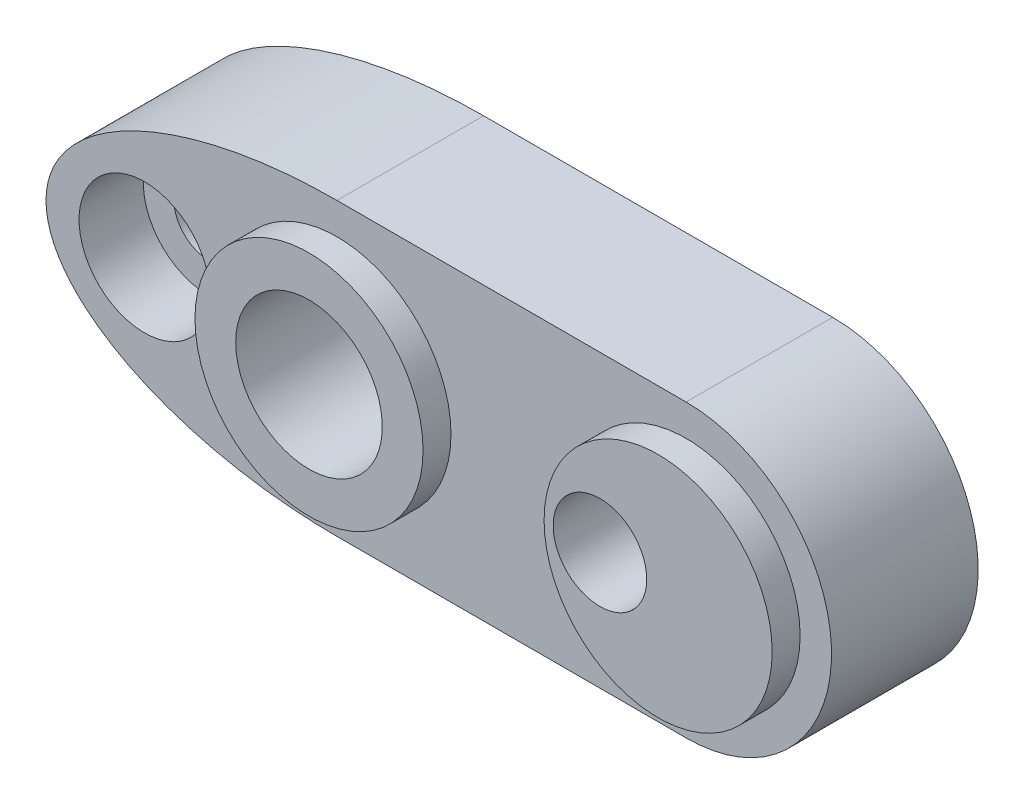
SolidWorks part; units mm, degrees
ref_plane "Front" through (0, 0, 0) normal (0, 0, 1) x (1, 0, 0)
ref_plane "Top" through (0, 0, 0) normal (0, 1, 0) x (1, 0, 0)
ref_plane "Right" through (0, 0, 0) normal (1, 0, 0) x (0, 0, -1)
sketch "Sketch1" plane through (0, 0, 0) normal (0, 0, 1) x (1, 0, 0)
  line L0 (0, 7.9375) -> (19.05, 7.9375)
  line L3 (0, -7.9375) -> (19.05, -7.9375)
  arc A2 (0, 7.9375) -> (0, -7.9375) centre (0, 0) ccw construction
  arc A3 (19.05, -7.9375) -> (19.05, 7.9375) centre (19.05, 0) ccw
  ellipse E0 centre (0, 0) end of major axis (-15.875, 0) minor radius 7.9375 (0, 7.9375) -> (0, -7.9375) ccw
  point P1 (0, 0)
  point P14 (-15.049, 2.188)
  point P15 (0, 0)
  dimension "D1" = 19.05
  dimension "D2" = 15.875
  dimension "D3" = 15.875
extrude "Boss-Extrude1" add sketch "Sketch1" against normal blind 9.525
sketch "Sketch2" plane through (0, 0, 0) normal (0, 0, 1) x (1, 0, 0)
  circle A0 centre (0, 0) radius 6.223
  circle A1 centre (19.05, 0) radius 6.223
  point P6 (0, 0)
  point P7 (0, 0)
  point P8 (19.05, -0.4001)
  point P9 (19.05, 0)
  dimension "D1" = 12.446
extrude "Cut-Extrude1" cut sketch "Sketch2" against normal blind 1.524 flip side to cut
sketch "Sketch3" plane through (0, 0, -9.525) normal (0, 0, -1) x (-1, 0, 0)
  circle A0 centre (0, 0) radius 4
  dimension "D1" = 8
extrude "Cut-Extrude2" cut sketch "Sketch3" against normal through all
hole_wizard "CBORE for #6 Socket Head Cap Screw1" positions "Sketch5" profile "Sketch6" counterbore size "#6" standard "ANSI Inch" end condition through all
sketch "Sketch5" plane through (0, 0, -1.524) normal (0, 0, 1) x (1, 0, 0)
  point P0 (-10.5, 0)
  point P4 (0, 0)
  dimension "D1" = 10.5
sketch "Sketch6" plane through (-10.5, 0, -1.524) normal (1, 0, 0) x (0, -1, 0)
  line L0 (0, 0) -> (0, 8.001)
  line L1 (0, 8.001) -> (1.8986, 8.001)
  line L3 (1.8986, 8.001) -> (1.8986, 3.5052)
  line L4 (1.8986, 3.5052) -> (3.5725, 3.5052)
  line L5 (3.5725, 3.5052) -> (3.5725, 0)
  line L7 (3.5725, 0) -> (0, 0)
  line L11 (0, -6.35) -> (0, 107.95) construction
  dimension "Thru Hole Dia." = 3.7973
  dimension "Thru Hole Depth" = 8.001
  dimension "C'Bore Dia." = 7.145
  dimension "C'Bore Depth" = 3.5052
hole_wizard "1/4-20 Tapped Hole1" positions "Sketch7" profile "Sketch8" tap size "1/4-20" standard "ANSI Inch" end condition through all
sketch "Sketch7" plane through (0, 0, 0) normal (0, 0, 1) x (1, 0, 0)
  circle A0 centre (19.05, 0) radius 6.223 construction
  point P0 (15.875, 0)
  point P5 (0, 0)
  dimension "D1" = 3.175
sketch "Sketch8" plane through (15.875, 0, 0) normal (1, 0, 0) x (0, -1, 0)
  line L0 (0, 0) -> (0, 9.525)
  line L1 (0, 9.525) -> (2.5527, 9.525)
  line L2 (2.5527, 9.525) -> (2.5527, 0)
  line L5 (2.5527, 0) -> (0, 0)
  line L11 (0, -6.35) -> (0, 107.95) construction
  dimension "Thru Tap Drill Dia." = 5.1054
  dimension "Thru Tap Drill Depth" = 9.525
cosmetic thread "Hole Thread1" parameters "D2"=6.35
